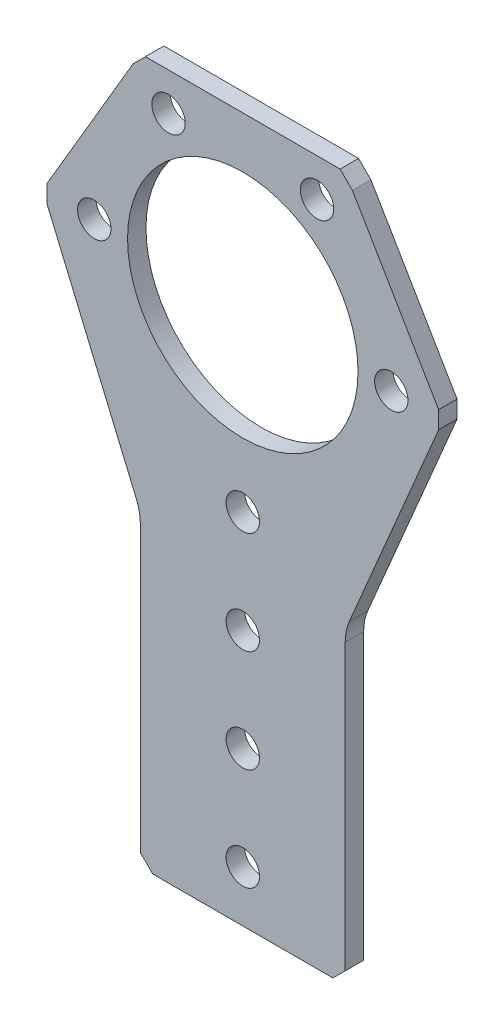
SolidWorks part; units mm, degrees
ref_plane "Front Plane" through (0, 0, 0) normal (0, 0, 1) x (1, 0, 0)
ref_plane "Top Plane" through (0, 0, 0) normal (0, 1, 0) x (1, 0, 0)
ref_plane "Right Plane" through (0, 0, 0) normal (1, 0, 0) x (0, 0, -1)
ref_plane "Plane1" through (0, 0, 2.286) normal (0, 0, 1) x (1, 0, 0)
sketch "Sketch1" plane through (0, 0, 2.286) normal (0, 0, 1) x (1, 0, 0)
  line L0 (-24.2821, -1.2536) -> (-13.2036, -27.387)
  line L1 (-12.7, -29.8654) -> (-12.7, -65.1484)
  line L2 (-12.7, -65.1484) -> (-11.1734, -66.675)
  line L3 (-11.1734, -66.675) -> (11.1734, -66.675)
  line L4 (11.1734, -66.675) -> (12.7, -65.1484)
  line L5 (12.7, -65.1484) -> (12.7, -29.8654)
  line L6 (13.2036, -27.387) -> (24.2821, -1.2536)
  line L7 (24.2821, -1.2536) -> (24.2821, 0.9054)
  line L8 (24.2821, 0.9054) -> (13.5961, 19.1109)
  line L9 (13.5961, 19.1109) -> (12.0694, 20.6375)
  line L10 (12.0694, 20.6375) -> (-12.0694, 20.6375)
  line L11 (-12.0694, 20.6375) -> (-13.5961, 19.1109)
  line L12 (-13.5961, 19.1109) -> (-24.2821, 0.9054)
  line L13 (-24.2821, 0.9054) -> (-24.2821, -1.2536)
  arc A0 (-13.2036, -27.387) -> (-12.7, -29.8654) centre (-19.05, -29.8654) cw
  arc A1 (12.7, -29.8654) -> (13.2036, -27.387) centre (19.05, -29.8654) cw
  circle A2 centre (-9.2075, 15.9479) radius 2.0701
  circle A3 centre (-18.415, 0) radius 2.0701
  circle A4 centre (0, -47.625) radius 2.0701
  circle A5 centre (0, -22.225) radius 2.0701
  circle A6 centre (0, 0) radius 14.2875
  circle A7 centre (0, -34.925) radius 2.0701
  circle A8 centre (0, -60.325) radius 2.0701
  circle A9 centre (18.415, 0) radius 2.0701
  circle A10 centre (9.2075, 15.9479) radius 2.0701
extrude "Boss-Extrude1" add sketch "Sketch1" against normal blind 2.286
